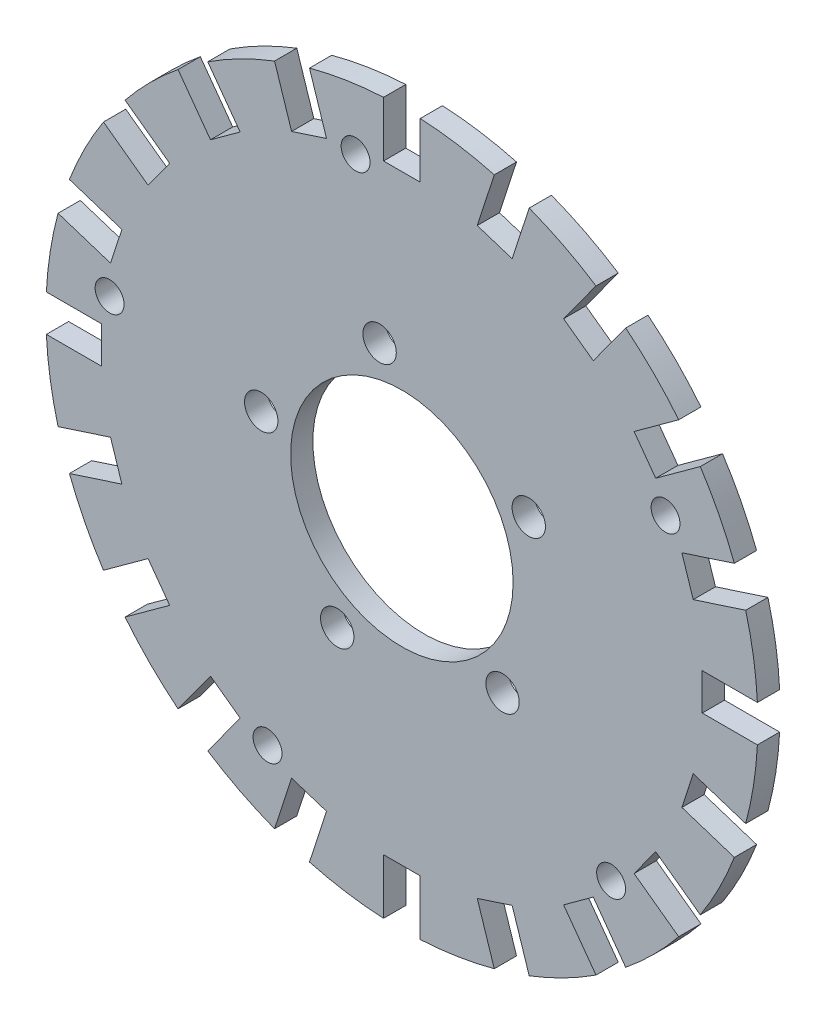
SolidWorks part; units mm, degrees
ref_plane "Plan de face" through (0, 0, 0) normal (0, 0, 1) x (1, 0, 0)
ref_plane "Plan de dessus" through (0, 0, 0) normal (0, 1, 0) x (1, 0, 0)
ref_plane "Plan de droite" through (0, 0, 0) normal (1, 0, 0) x (0, 0, -1)
sketch "Esquisse1" plane through (0, 0, 0) normal (0, 0, 1) x (1, 0, 0)
  circle A0 centre (0, 0) radius 160
  circle A1 centre (0, 0) radius 50
  dimension "D1" = 320
  dimension "D2" = 100
extrude "Boss.-Extru.1" add sketch "Esquisse1" along normal mid plane 10
sketch "Esquisse2" plane through (0, 0, 5) normal (0, 0, 1) x (1, 0, 0)
  line L0 (-10.0118, 63.2121) -> (0, 0) construction
  line L1 (0, 0) -> (0, 76.252) construction
  circle A0 centre (0, 0) radius 64 construction
  circle A1 centre (-10.0118, 63.2121) radius 7.5
  dimension "D1" = 15
  dimension "D2" = 128
  dimension "D3" = 9
extrude "Enlèv. mat.-Extru.1" cut sketch "Esquisse2" against normal through all
sketch "Esquisse3" plane through (0, 0, 5) normal (0, 0, 1) x (1, 0, 0)
  line L1 (-8.25, 135) -> (8.25, 135)
  line L2 (-8.25, 135) -> (-8.25, 160)
  line L3 (-8.25, 160) -> (8.25, 160)
  line L4 (8.25, 135) -> (8.25, 160)
  line L5 (-8.25, 135) -> (8.25, 160) construction
  line L6 (-8.25, 160) -> (8.25, 135) construction
  circle A0 centre (0, 0) radius 160 construction
  point P0 (0, 147.5)
  dimension "D2" = 16.5
  dimension "D1" = 25
extrude "Enlèv. mat.-Extru.2" cut sketch "Esquisse3" against normal through all
sketch "Esquisse4" plane through (0, 0, 5) normal (0, 0, 1) x (1, 0, 0)
  line L0 (-20.8058, 131.3625) -> (0, 0) construction
  line L1 (-8.25, 159.7872) -> (-8.25, 135) construction
  circle A0 centre (-20.8058, 131.3625) radius 6.5
  dimension "D1" = 9
  dimension "D2" = 13
  dimension "D3" = 133
extrude "Enlèv. mat.-Extru.3" cut sketch "Esquisse4" against normal through all
pattern_circular "Répétition circulaire1" count 5 over 360 about axis through (0, 0, 0) along (0, 0, 1) of "Enlèv. mat.-Extru.1", "Enlèv. mat.-Extru.3"
pattern_circular "Répétition circulaire2" count 20 over 360 about axis through (0, 0, 0) along (0, 0, 1) of "Enlèv. mat.-Extru.2"
